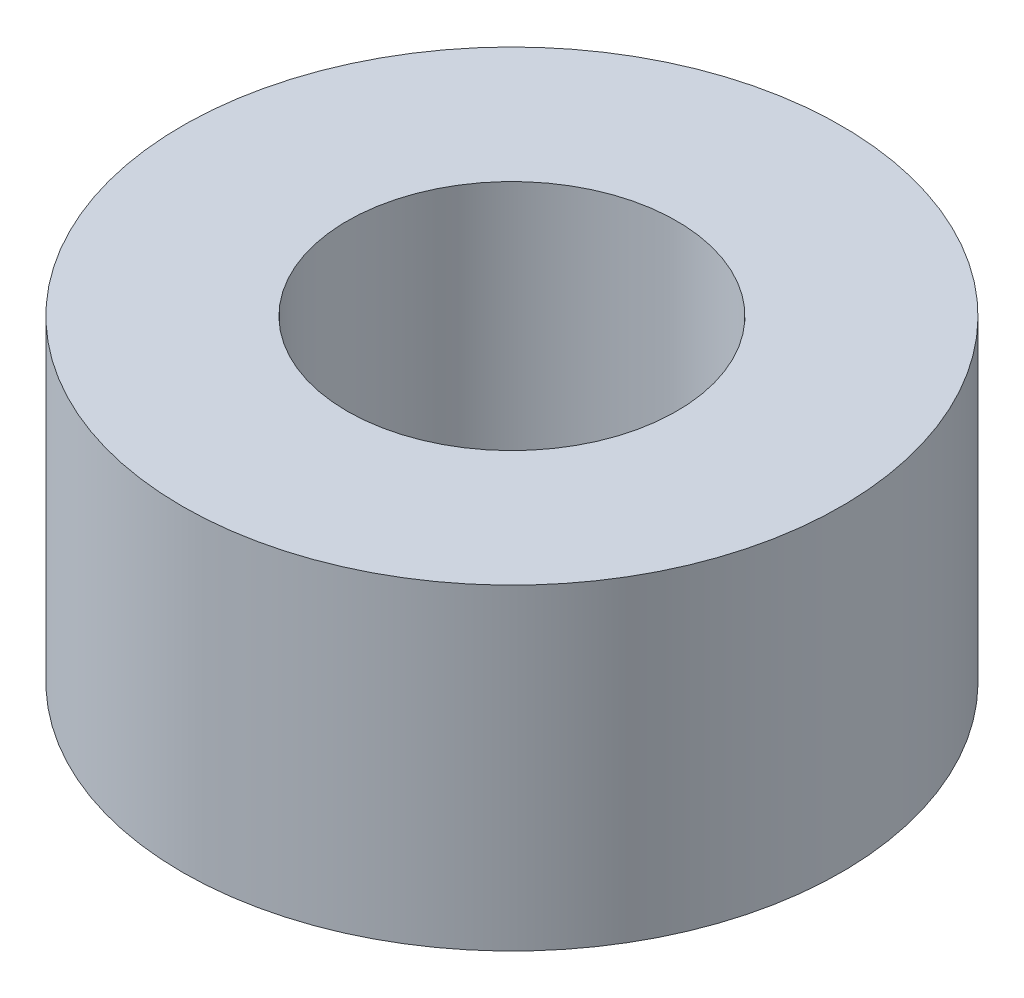
SolidWorks part; units mm, degrees
ref_plane "Front Plane" through (0, 0, 0) normal (0, 0, 1) x (1, 0, 0)
ref_plane "Top Plane" through (0, 0, 0) normal (0, 1, 0) x (1, 0, 0)
ref_plane "Right Plane" through (0, 0, 0) normal (1, 0, 0) x (0, 0, -1)
sketch "Sketch1" plane through (0, 0, 0) normal (0, 1, 0) x (1, 0, 0)
  circle A0 centre (0, 0) radius 1.651
  circle A1 centre (0, 0) radius 3.302
  dimension "D1" = 3.302
  dimension "D2" = 6.604
extrude "Boss-Extrude1" add sketch "Sketch1" along normal blind 3.175
